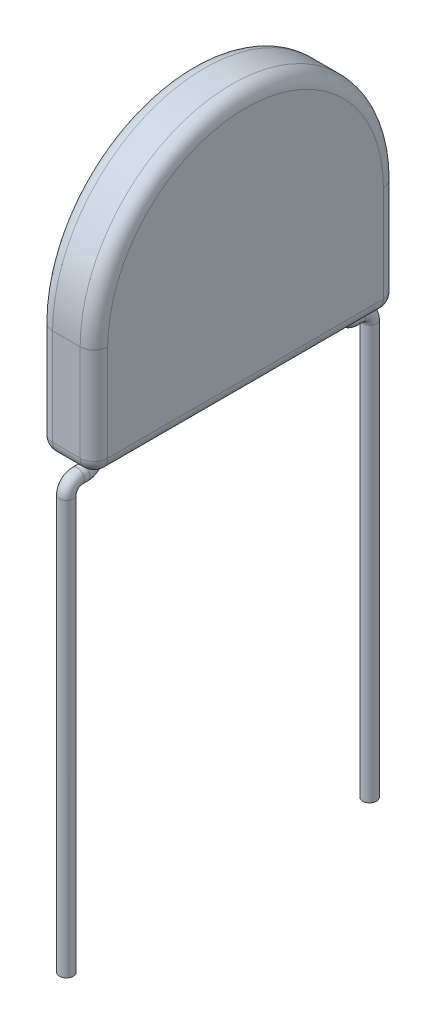
SolidWorks part; units mm, degrees
material "Copper"
ref_plane "Front" through (0, 0, 0) normal (0, 0, 1) x (1, 0, 0)
ref_plane "Top" through (0, 0, 0) normal (0, 1, 0) x (1, 0, 0)
ref_plane "Right" through (0, 0, 0) normal (1, 0, 0) x (0, 0, -1)
sketch "Sketch1" plane through (0, 0, 0) normal (1, 0, 0) x (0, 0, -1)
  line L0 (0, 2) -> (0, 0)
  line L1 (0, 0) -> (5.5, 0)
  line L2 (5.5, 0) -> (5.5, 2)
  arc A0 (5.5, 2) -> (0, 2) centre (2.75, 2) ccw
  dimension "D1" = 5.5
  dimension "D2" = 2
extrude "Boss-Extrude1" add sketch "Sketch1" along normal blind 1
fillet "Fillet3" radius 0.25 10 edges at (0, 1, 0) (0, 4.75, -2.75) (1, 1, -5.5) (1, 1, 0) (0, 1, -5.5) (0.5, 0, -5.5) (0, 0, -2.75) (1, 0, -2.75) (0.5, 0, 0) (1, 4.75, -2.75)
ref_plane "Plane1" through (0.5, 0, 0) normal (1, 0, 0) x (0, 0, -1)
sketch "Sketch2" plane through (0.5, 0, 0) normal (1, 0, 0) x (0, 0, -1)
  line L0 (0.5, 0) -> (0.5, -0.05)
  line L1 (0.3, -0.25) -> (0.2, -0.25)
  line L2 (0, -0.45) -> (0, -7.95)
  line L3 (5.25, 0) -> (0.25, 0) construction
  arc A0 (0.2, -0.25) -> (0, -0.45) centre (0.2, -0.45) ccw
  arc A1 (0.5, -0.05) -> (0.3, -0.25) centre (0.3, -0.05) cw
  dimension "D1" = 0.2
  dimension "D4" = 0.25
  dimension "D2" = 0.5
  dimension "D3" = 7.5
sketch "Sketch3" plane through (0, 0, 0) normal (0, -1, 0) x (1, 0, 0)
  circle A0 centre (0.5, -0.5) radius 0.125
  dimension "D1" = 0.25
sweep "Sweep1" add profiles "Sketch3" path "Sketch2"
ref_plane "Plane2" through (0, 0, -2.75) normal (0, 0, 1) x (1, 0, 0)
mirror "Mirror1" about plane through (0, 0, -2.75) normal (0, 0, 1) of "Sweep1"
